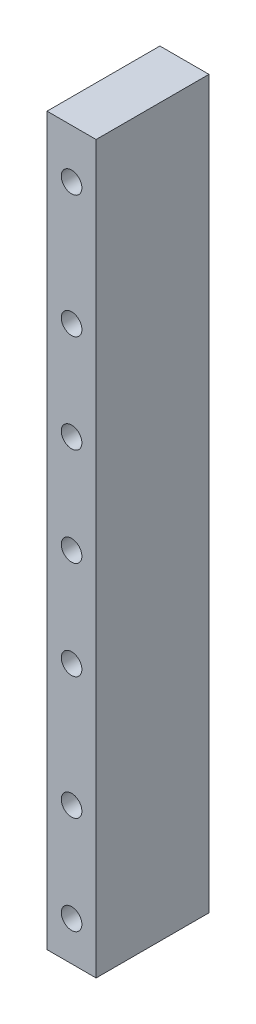
SolidWorks part; units mm, degrees
ref_plane "Front Plane" through (0, 0, 0) normal (0, 0, 1) x (1, 0, 0)
ref_plane "Top Plane" through (0, 0, 0) normal (0, 1, 0) x (1, 0, 0)
ref_plane "Right Plane" through (0, 0, 0) normal (1, 0, 0) x (0, 0, -1)
sketch "Sketch1" plane through (0, 0, 0) normal (0, 0, 1) x (1, 0, 0)
  line L0 (-75, 95.4) -> (-75, -10.4) construction
  line L1 (-80, 42.5) -> (-70, 42.5)
  line L2 (-80, 42.5) -> (-80, -42.5)
  line L3 (-80, -42.5) -> (-70, -42.5)
  line L4 (-70, 42.5) -> (-70, -42.5)
  line L5 (-78.6, -30.4) -> (-75, -28.4)
  line L7 (-78.6, -34.6) -> (-78.6, -30.4)
  line L9 (-71.4, -34.6) -> (-71.4, -30.4)
  line L10 (-80, 0) -> (-70, 0) construction
  line L11 (-75, -22.5) -> (-70, -22.5) construction
  line L12 (-71.4, -30.4) -> (-75, -28.4)
  line L13 (-75, -36.6) -> (-75, -42.5) construction
  line L14 (-71.4, -34.6) -> (-75, -36.6)
  line L15 (-78.6, -34.6) -> (-75, -36.6)
  line L16 (-78.6, -10.4) -> (-75, -8.4)
  line L17 (-71.4, -10.4) -> (-75, -8.4)
  line L18 (-71.4, -10.4) -> (-71.4, -14.6)
  line L19 (-71.4, -14.6) -> (-75, -16.6)
  line L20 (-78.6, -14.6) -> (-75, -16.6)
  line L21 (-78.6, -10.4) -> (-78.6, -14.6)
  line L22 (-78.6, 34.6) -> (-75, 36.6)
  line L23 (-71.4, 34.6) -> (-75, 36.6)
  line L24 (-71.4, 34.6) -> (-71.4, 30.4)
  line L25 (-71.4, 30.4) -> (-75, 28.4)
  line L26 (-78.6, 30.4) -> (-75, 28.4)
  line L27 (-78.6, 34.6) -> (-78.6, 30.4)
  line L28 (-78.6, 10.4) -> (-78.6, 14.6)
  line L29 (-78.6, 14.6) -> (-75, 16.6)
  line L30 (-71.4, 14.6) -> (-75, 16.6)
  line L31 (-71.4, 10.4) -> (-71.4, 14.6)
  line L32 (-71.4, 10.4) -> (-75, 8.4)
  line L33 (-78.6, 10.4) -> (-75, 8.4)
  line L34 (-75, 121.6) -> (-75, 127.5) construction
  line L35 (-75, 107.5) -> (-70, 107.5) construction
  line L36 (-80, 85) -> (-70, 85) construction
  line L37 (-78.6, 74.6) -> (-75, 76.6)
  line L38 (-71.4, 74.6) -> (-75, 76.6)
  line L39 (-71.4, 74.6) -> (-71.4, 70.4)
  line L40 (-71.4, 70.4) -> (-75, 68.4)
  line L41 (-78.6, 70.4) -> (-75, 68.4)
  line L42 (-78.6, 74.6) -> (-78.6, 70.4)
  line L43 (-78.6, 50.4) -> (-78.6, 54.6)
  line L44 (-78.6, 54.6) -> (-75, 56.6)
  line L45 (-71.4, 54.6) -> (-75, 56.6)
  line L46 (-71.4, 50.4) -> (-71.4, 54.6)
  line L47 (-71.4, 50.4) -> (-75, 48.4)
  line L48 (-78.6, 50.4) -> (-75, 48.4)
  line L49 (-78.6, 95.4) -> (-78.6, 99.6)
  line L50 (-78.6, 99.6) -> (-75, 101.6)
  line L51 (-71.4, 99.6) -> (-75, 101.6)
  line L52 (-71.4, 95.4) -> (-71.4, 99.6)
  line L53 (-71.4, 95.4) -> (-75, 93.4)
  line L54 (-78.6, 95.4) -> (-75, 93.4)
  line L55 (-78.6, 119.6) -> (-75, 121.6)
  line L56 (-71.4, 119.6) -> (-75, 121.6)
  line L57 (-71.4, 115.4) -> (-75, 113.4)
  line L58 (-71.4, 119.6) -> (-71.4, 115.4)
  line L59 (-78.6, 119.6) -> (-78.6, 115.4)
  line L60 (-78.6, 115.4) -> (-75, 113.4)
  line L61 (-70, 42.5) -> (-70, 127.5)
  line L62 (-80, 127.5) -> (-70, 127.5)
  line L63 (-80, 42.5) -> (-80, 127.5)
  circle A0 centre (-75, 32.5) radius 2.1
  circle A1 centre (-75, 12.5) radius 2.1
  circle A2 centre (-75, -12.5) radius 2.1
  circle A3 centre (-75, -32.5) radius 2.1
  circle A4 centre (-75, -12.5) radius 2.1
  circle A5 centre (-75, 12.5) radius 2.1
  circle A6 centre (-75, 32.5) radius 2.1
  circle A7 centre (-75, 52.5) radius 2.1
  circle A8 centre (-75, 72.5) radius 2.1
  circle A9 centre (-75, 97.5) radius 2.1
  circle A10 centre (-75, 117.5) radius 2.1
  circle A11 centre (-75, 97.5) radius 2.1
  circle A12 centre (-75, 72.5) radius 2.1
  circle A13 centre (-75, 52.5) radius 2.1
  point P58 (-75, 42.5)
  dimension "D1" = 10
  dimension "D2" = 7.2
  dimension "D3" = 4.2
extrude "Boss-Extrude2" add sketch "Sketch1" along normal blind 5 contours L4 L1 L2 L3 L33 L28 L29 L30 L31 L32 L27 L22 L23 L24 L25 L26 L21 L16 L17 L18 L19 L20 L15 L7 L5 L12 L9 L14 | L63 L1 L61 L62 L60 L59 L55 L56 L58 L57 L54 L49 L50 L51 L52 L53 L48 L43 L44 L45 L46 L47 L42 L37 L38 L39 L40 L41
sketch "Sketch2" plane through (0, 0, 0) normal (0, 0, -1) x (-1, 0, 0)
  line L1 (70, 127.5) -> (80, 127.5)
  line L2 (70, 127.5) -> (70, -42.5)
  line L3 (70, -42.5) -> (80, -42.5)
  line L4 (80, 127.5) -> (80, -42.5)
extrude "Cut-Extrude1" cut sketch "Sketch2" against normal blind 1
sketch "Sketch3" plane through (0, 0, 1) normal (0, 0, -1) x (-1, 0, 0)
  line L0 (75, 113.4) -> (80, 113.4)
  line L1 (80, -42.5) -> (80, 127.5) construction
  line L2 (75, 121.6) -> (80, 121.6)
  line L3 (75, 101.6) -> (80, 101.6)
  line L4 (80, 121.6) -> (80, 113.4)
  line L5 (75, 93.4) -> (80, 93.4)
  line L6 (80, 93.4) -> (80, 101.6)
  line L7 (75, 76.6) -> (80, 76.6)
  line L8 (80, 76.6) -> (80, 68.4)
  line L9 (80, 68.4) -> (75, 68.4)
  line L10 (75, 56.6) -> (80, 56.6)
  line L11 (80, 56.6) -> (80, 48.4)
  line L12 (80, 48.4) -> (75, 48.4)
  line L13 (70, 42.5) -> (80, 42.5) construction
  line L14 (70, 127.5) -> (70, -42.5) construction
  line L15 (80, 36.6) -> (75, 36.6)
  line L16 (80, 28.4) -> (80, 36.6)
  line L17 (75, 28.4) -> (80, 28.4)
  line L18 (80, 16.6) -> (75, 16.6)
  line L19 (80, 8.4) -> (80, 16.6)
  line L20 (75, 8.4) -> (80, 8.4)
  line L21 (75, -8.4) -> (80, -8.4)
  line L22 (80, -8.4) -> (80, -16.6)
  line L23 (75, -16.6) -> (80, -16.6)
  line L24 (75, -28.4) -> (80, -28.4)
  line L25 (80, -36.6) -> (80, -28.4)
  line L26 (75, -36.6) -> (80, -36.6)
  line L27 (75, 121.6) -> (75, 113.4)
  line L28 (75, 101.6) -> (75, 93.4)
  line L29 (75, 76.6) -> (75, 68.4)
  line L30 (75, 56.6) -> (75, 48.4)
  line L31 (75, 36.6) -> (75, 28.4)
  line L32 (75, 16.6) -> (75, 8.4)
  line L33 (75, -8.4) -> (75, -16.6)
  line L34 (75, -28.4) -> (75, -36.6)
extrude "Cut-Extrude2" cut sketch "Sketch3" against normal blind 4
sketch "Sketch5" plane through (0, 0, 5) normal (0, 0, 1) x (1, 0, 0)
  line L0 (-80, 127.5) -> (-70, 127.5)
  line L1 (-70, 127.5) -> (-70, -42.5)
  line L2 (-70, -42.5) -> (-80, -42.5)
  line L3 (-80, -42.5) -> (-80, -36.6)
  line L4 (-80, 121.6) -> (-75, 121.6)
  line L5 (-75, 121.6) -> (-71.4, 119.6)
  line L6 (-71.4, 119.6) -> (-71.4, 115.4)
  line L7 (-71.4, 115.4) -> (-75, 113.4)
  line L8 (-75, 113.4) -> (-80, 113.4)
  line L9 (-80, 101.6) -> (-75, 101.6)
  line L10 (-75, 101.6) -> (-71.4, 99.6)
  line L11 (-71.4, 99.6) -> (-71.4, 95.4)
  line L12 (-71.4, 95.4) -> (-75, 93.4)
  line L13 (-75, 93.4) -> (-80, 93.4)
  line L14 (-80, 76.6) -> (-75, 76.6)
  line L15 (-75, 76.6) -> (-71.4, 74.6)
  line L16 (-71.4, 74.6) -> (-71.4, 70.4)
  line L17 (-71.4, 70.4) -> (-75, 68.4)
  line L18 (-75, 68.4) -> (-80, 68.4)
  line L19 (-80, 56.6) -> (-75, 56.6)
  line L20 (-75, 56.6) -> (-71.4, 54.6)
  line L21 (-71.4, 54.6) -> (-71.4, 50.4)
  line L22 (-71.4, 50.4) -> (-75, 48.4)
  line L23 (-75, 48.4) -> (-80, 48.4)
  line L24 (-80, 36.6) -> (-75, 36.6)
  line L25 (-75, 36.6) -> (-71.4, 34.6)
  line L26 (-71.4, 34.6) -> (-71.4, 30.4)
  line L27 (-71.4, 30.4) -> (-75, 28.4)
  line L28 (-75, 28.4) -> (-80, 28.4)
  line L29 (-80, 16.6) -> (-75, 16.6)
  line L30 (-75, 16.6) -> (-71.4, 14.6)
  line L31 (-71.4, 14.6) -> (-71.4, 10.4)
  line L32 (-71.4, 10.4) -> (-75, 8.4)
  line L33 (-75, 8.4) -> (-80, 8.4)
  line L34 (-80, -8.4) -> (-75, -8.4)
  line L35 (-75, -8.4) -> (-71.4, -10.4)
  line L36 (-71.4, -10.4) -> (-71.4, -14.6)
  line L37 (-71.4, -14.6) -> (-75, -16.6)
  line L38 (-75, -16.6) -> (-80, -16.6)
  line L39 (-80, -28.4) -> (-75, -28.4)
  line L40 (-75, -28.4) -> (-71.4, -30.4)
  line L41 (-71.4, -30.4) -> (-71.4, -34.6)
  line L42 (-71.4, -34.6) -> (-75, -36.6)
  line L43 (-75, -36.6) -> (-80, -36.6)
  line L44 (-80, 56.6) -> (-80, 127.5)
  line L45 (-80, 36.6) -> (-80, 48.4)
  line L46 (-80, 16.6) -> (-80, 28.4)
  line L47 (-80, -8.4) -> (-80, 8.4)
  line L48 (-80, -28.4) -> (-80, -16.6)
extrude "Boss-Extrude3" add sketch "Sketch5" along normal blind 9 contours L48 L39 L40 L41 L42 L43 L3 L2 L1 L0 L44 L4 L5 L6 L7 L8 L9 L10 L11 L12 L13 L14 L15 L16 L17 L18 L19 L20 L21 L22 L23 L45 L24 L25 L26 L27 L28 L46 L29 L30 L31 L32 L33 L47 L34 L35 L36 L37
sketch "Sketch6" plane through (-80, 0, 0) normal (-1, 0, 0) x (0, 0, 1)
  line L0 (14, 127.5) -> (1, 127.5) construction
  line L1 (5, 127.5) -> (10, 127.5)
  line L2 (5, 127.5) -> (5, -42.5)
  line L3 (5, -42.5) -> (10, -42.5)
  line L4 (10, 127.5) -> (10, -42.5)
  line L5 (14, -42.5) -> (1, -42.5) construction
  line L6 (1, 56.6) -> (1, 68.4) construction
  line L7 (14, -28.4) -> (14, -16.6) construction
  dimension "D1" = 4
  dimension "D2" = 4
extrude "Boss-Extrude4" add sketch "Sketch6" against normal blind 10
sketch "Sketch7" plane through (0, 0, 14) normal (0, 0, 1) x (1, 0, 0)
  line L1 (-80, 127.5) -> (-70, 127.5)
  line L2 (-80, 127.5) -> (-80, -42.5)
  line L3 (-80, -42.5) -> (-70, -42.5)
  line L4 (-70, 127.5) -> (-70, -42.5)
extrude "Boss-Extrude6" add sketch "Sketch7" along normal blind 5 contours L2 L1 L4 L3
sketch "Sketch9" plane through (0, 0, 1) normal (0, 0, -1) x (-1, 0, 0)
  line L1 (70, 127.5) -> (80, 127.5)
  line L2 (70, 127.5) -> (70, -42.5)
  line L3 (70, -42.5) -> (80, -42.5)
  line L4 (80, 127.5) -> (80, -42.5)
extrude "Boss-Extrude7" add sketch "Sketch9" along normal blind 5
sketch "Sketch10" plane through (0, 0, 19) normal (0, 0, 1) x (1, 0, 0)
  circle A0 centre (-75, 117.5) radius 2.1
  circle A1 centre (-75, 97.5) radius 2.1
  circle A2 centre (-75, 72.5) radius 2.1
  circle A3 centre (-75, 52.5) radius 2.1
  circle A4 centre (-75, 32.5) radius 2.1
  circle A5 centre (-75, 12.5) radius 2.1
  circle A6 centre (-75, -12.5) radius 2.1
  circle A7 centre (-75, -32.5) radius 2.1
extrude "Cut-Extrude3" cut sketch "Sketch10" against normal blind 39
sketch "Sketch13" plane through (0, 0, -4) normal (0, 0, -1) x (-1, 0, 0)
  line L0 (75, 107.5) -> (75, 97.5) construction
  line L2 (70, 127.5) -> (75, 127.5)
  line L3 (70, 127.5) -> (70, 107.5)
  line L4 (70, 107.5) -> (75, 107.5)
  line L6 (80, 127.5) -> (75, 127.5)
  line L7 (80, 127.5) -> (80, 107.5)
  line L8 (80, 107.5) -> (75, 107.5)
extrude "Cut-Extrude6" cut sketch "Sketch13" against normal blind 39
sketch "Sketch14" plane through (0, 0, -4) normal (0, 0, -1) x (-1, 0, 0)
  line L0 (80, -42.5) -> (80, 107.5) construction
  line L1 (70, -42.5) -> (80, -42.5)
  line L2 (70, -42.5) -> (70, -40.5)
  line L3 (70, -40.5) -> (80, -40.5)
  line L4 (80, -42.5) -> (80, -40.5)
  dimension "D1" = 2
extrude "Cut-Extrude7" cut sketch "Sketch14" against normal blind 39
